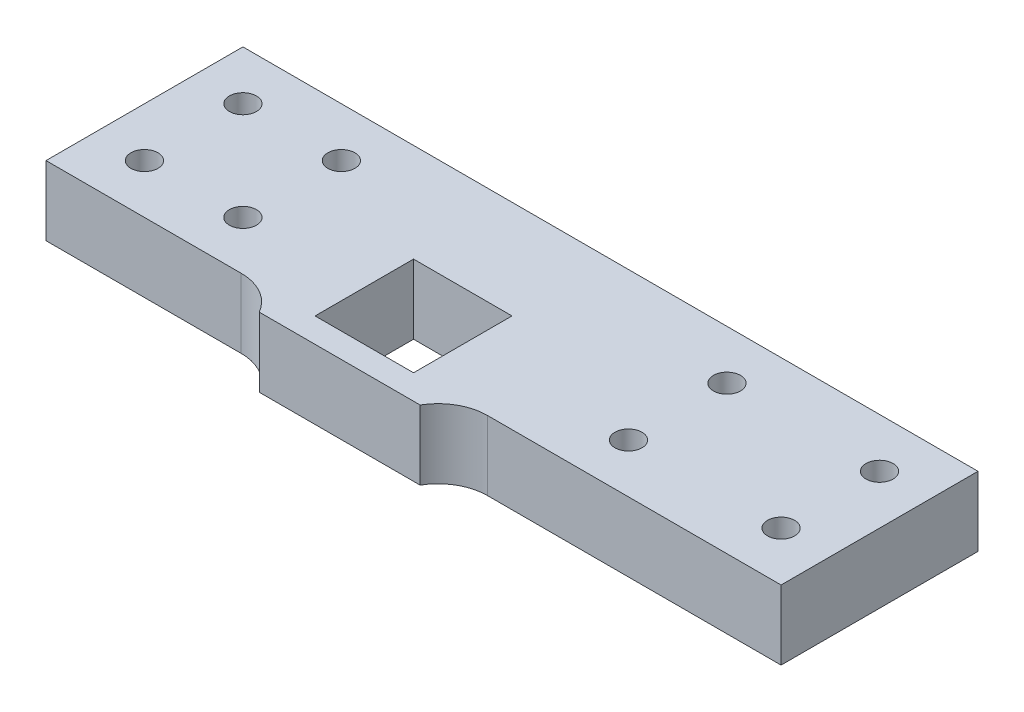
SolidWorks part; units mm, degrees
ref_plane "Front Plane" through (0, 0, 0) normal (0, 0, 1) x (1, 0, 0)
ref_plane "Top Plane" through (0, 0, 0) normal (0, 1, 0) x (1, 0, 0)
ref_plane "Right Plane" through (0, 0, 0) normal (1, 0, 0) x (0, 0, -1)
sketch "Sketch1" plane through (0, 0, 0) normal (0, 1, 0) x (1, 0, 0)
  line L0 (10, -17.5) -> (-10, -17.5)
  line L1 (-10, -17.5) -> (-10, 2.5)
  line L2 (10, 2.5) -> (10, -17.5)
  line L3 (10, 2.5) -> (-10, 2.5)
  line L4 (10, -22.5) -> (16.3397, -22.5)
  line L5 (25, -17.5) -> (64.66, -17.5)
  line L6 (64.66, -17.5) -> (64.66, 22.5)
  line L7 (64.66, 22.5) -> (-64.66, 22.5)
  line L8 (-64.66, 22.5) -> (-64.66, -17.5)
  line L9 (-64.66, -17.5) -> (-25, -17.5)
  line L10 (-16.3397, -22.5) -> (-10, -22.5)
  line L11 (-10, -22.5) -> (10, -22.5)
  arc A0 (25, -17.5) -> (16.3397, -22.5) centre (25, -27.5) ccw
  arc A1 (-16.3397, -22.5) -> (-25, -17.5) centre (-25, -27.5) ccw
  circle A2 centre (34.66, 12.5) radius 2.75
  circle A3 centre (34.66, -7.5) radius 2.75
  circle A4 centre (54.66, -7.5) radius 2.75
  circle A5 centre (54.66, 12.5) radius 2.75
  circle A6 centre (-54.66, -7.5) radius 2.75
  circle A7 centre (-34.66, 12.5) radius 2.75
  circle A8 centre (-54.66, 12.5) radius 2.75
  circle A9 centre (-34.66, -7.5) radius 2.75
  point P32 (0, 0)
extrude "Boss-Extrude1" add sketch "Sketch1" along normal blind 14.1
other "Move Face1" face at (64.66, 7.05, -2.5) parameters "D1"=20
sketch "Sketch6" plane through (0, 0, 0) normal (0, -1, 0) x (1, 0, 0)
  line L1 (28.3527, 14.3795) -> (59.34, 14.3795)
  line L2 (28.3527, 14.3795) -> (28.3527, -18.8096)
  line L3 (28.3527, -18.8096) -> (59.34, -18.8096)
  line L4 (59.34, 14.3795) -> (59.34, -18.8096)
extrude "Boss-Extrude2" add sketch "Sketch6" against normal up to surface (14.1 mm away) up to face at (-54.66, 14.1, -9.75)
hole_wizard "M5 Clearance Hole2" positions "Sketch7" profile "Sketch8" hole size "M5" standard "ANSI Metric" end condition through all
sketch "Sketch7" plane through (0, 0, 0) normal (0, -1, 0) x (-1, 0, 0)
  line L0 (-25, -17.5) -> (-84.66, -17.5) construction
  line L1 (-84.66, -17.5) -> (-84.66, 22.5) construction
  point P0 (-74.66, -7.5)
  point P12 (-43.66, -7.5)
  point P13 (-43.66, 12.5)
  point P14 (-74.66, 12.5)
  dimension "D1" = 10
  dimension "D2" = 10
  dimension "D3" = 2
  dimension "D4" = 2
sketch "Sketch8" plane through (74.66, 0, 7.5) normal (1, 0, 0) x (0, 0, -1)
  line L0 (0, 0) -> (0, 14.1)
  line L1 (0, 14.1) -> (2.75, 14.1)
  line L2 (2.75, 14.1) -> (2.75, 0)
  line L5 (2.75, 0) -> (0, 0)
  line L11 (0, -6.35) -> (0, 107.95) construction
  dimension "Thru Hole Dia." = 5.5
  dimension "Thru Hole Depth" = 14.1
